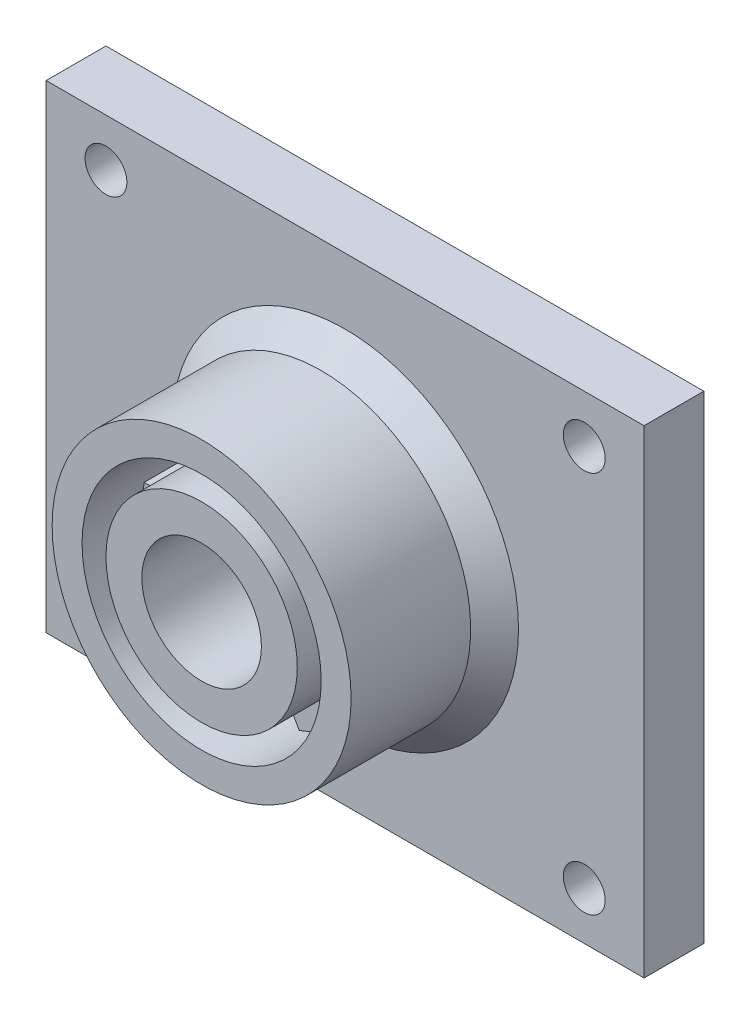
SolidWorks part; units mm, degrees
ref_plane "Alzado" through (0, 0, 0) normal (0, 0, 1) x (1, 0, 0)
ref_plane "Planta" through (0, 0, 0) normal (0, 1, 0) x (1, 0, 0)
ref_plane "Vista lateral" through (0, 0, 0) normal (1, 0, 0) x (0, 0, -1)
sketch "Croquis1" plane through (0, 0, 0) normal (0, 0, 1) x (1, 0, 0)
  line L0 (-20, 16) -> (20, 16) construction
  line L1 (-25, -20) -> (25, -20)
  line L2 (-25, -20) -> (-25, 20)
  line L3 (-25, 20) -> (25, 20)
  line L4 (25, -20) -> (25, 20)
  line L5 (-25, -20) -> (25, 20) construction
  line L6 (-25, 20) -> (25, -20) construction
  line L7 (-20, 16) -> (-20, -16) construction
  circle A0 centre (-20, 16) radius 1.75
  circle A1 centre (20, 16) radius 1.75
  circle A2 centre (20, -16) radius 1.75
  circle A3 centre (-20, -16) radius 1.75
  point P0 (0, 0)
  dimension "D3" = 3.5
  dimension "D5" = 2
  dimension "D1" = 50
  dimension "D2" = 40
  dimension "D4" = 4
  dimension "D6" = 2
extrude "Saliente-Extruir1" add sketch "Croquis1" along normal mid plane 5
sketch "Croquis2" plane through (0, 0, 2.5) normal (0, 0, 1) x (1, 0, 0)
  line L0 (-9.798, -2) -> (-7.746, -2)
  line L1 (-5, -8.6603) -> (5, 8.6603) construction
  line L8 (-5, 8.6603) -> (5, -8.6603) construction
  line L9 (-18.4242, 0) -> (18.4242, 0) construction
  line L10 (-9.798, 2) -> (-7.746, 2)
  line L11 (-3.1669, 9.4853) -> (-2.1409, 7.7082)
  line L12 (-6.631, 7.4853) -> (-5.605, 5.7082)
  line L13 (6.631, 7.4853) -> (5.605, 5.7082)
  line L14 (3.1669, 9.4853) -> (2.1409, 7.7082)
  line L15 (9.798, -2) -> (7.746, -2)
  line L16 (9.798, 2) -> (7.746, 2)
  line L17 (3.1669, -9.4853) -> (2.1409, -7.7082)
  line L18 (6.631, -7.4853) -> (5.605, -5.7082)
  line L19 (-6.631, -7.4853) -> (-5.605, -5.7082)
  line L20 (-3.1669, -9.4853) -> (-2.1409, -7.7082)
  line L21 (0, 0) -> (-7.746, 2) construction
  line L22 (0, 0) -> (-2.1409, 7.7082) construction
  circle A0 centre (0, 0) radius 10
  circle A1 centre (0, 0) radius 12.5
  circle A2 centre (0, 0) radius 8
  circle A3 centre (0, 0) radius 5
  dimension "D1" = 20
  dimension "D3" = 16
  dimension "D4" = 60
  dimension "D10" = 10
  dimension "D5" = 60
  dimension "D6" = 2
  dimension "D7" = 6
  dimension "D8" = 60
  dimension "D9" = 8
  dimension "D2" = 2.5
extrude "Saliente-Extruir2" add sketch "Croquis2" along normal blind 7 contours A2 L11 A0 L12 | A2 L13 A0 L14 | A2 L15 A0 L16 | A2 L17 A0 L18 | A2 L19 A0 L20 | A2 L10 A0 L0 | A1 A0 | A2 A3
sketch "Croquis4" plane through (0, 0, 9.5) normal (0, 0, 1) x (1, 0, 0)
  circle A0 centre (0, 0) radius 12.5 construction
  circle A1 centre (0, 0) radius 5
  circle A2 centre (0, 0) radius 5
  circle A3 centre (0, 0) radius 12.5
  circle A4 centre (0, 0) radius 10
  circle A7 centre (0, 0) radius 8
  circle A8 centre (0, 0) radius 8
  arc M4 (-7.746, -2) -> (-5.605, -5.7082) centre (0, 0) ccw
  arc M6 (-6.631, -7.4853) -> (-9.798, -2) centre (0, 0) cw
  arc M8 (-2.1409, -7.7082) -> (2.1409, -7.7082) centre (0, 0) ccw
  arc M10 (3.1669, -9.4853) -> (-3.1669, -9.4853) centre (0, 0) cw
  arc M12 (5.605, -5.7082) -> (7.746, -2) centre (0, 0) ccw
  arc M14 (9.798, -2) -> (6.631, -7.4853) centre (0, 0) cw
  arc M16 (7.746, 2) -> (5.605, 5.7082) centre (0, 0) ccw
  arc M18 (6.631, 7.4853) -> (9.798, 2) centre (0, 0) cw
  arc M20 (2.1409, 7.7082) -> (-2.1409, 7.7082) centre (0, 0) ccw
  arc M22 (-3.1669, 9.4853) -> (3.1669, 9.4853) centre (0, 0) cw
  arc M24 (-5.605, 5.7082) -> (-7.746, 2) centre (0, 0) ccw
  arc M26 (-9.798, 2) -> (-6.631, 7.4853) centre (0, 0) cw
  circle M27 centre (0, 0) radius 12.5
  circle M28 centre (0, 0) radius 5
  dimension "D1" = 0
  dimension "D2" = 2.5
  dimension "D3" = 3
extrude "Saliente-Extruir3" add sketch "Croquis4" along normal blind 5 contours A4 M27 M18 M14 M10 M6 M26 M22 | A8 M16 M20 M24 M4 M8 M12 M28
chamfer "Chaflán1" distance 2 angle 45 1 edges at (-12.5, 0, 2.5)
